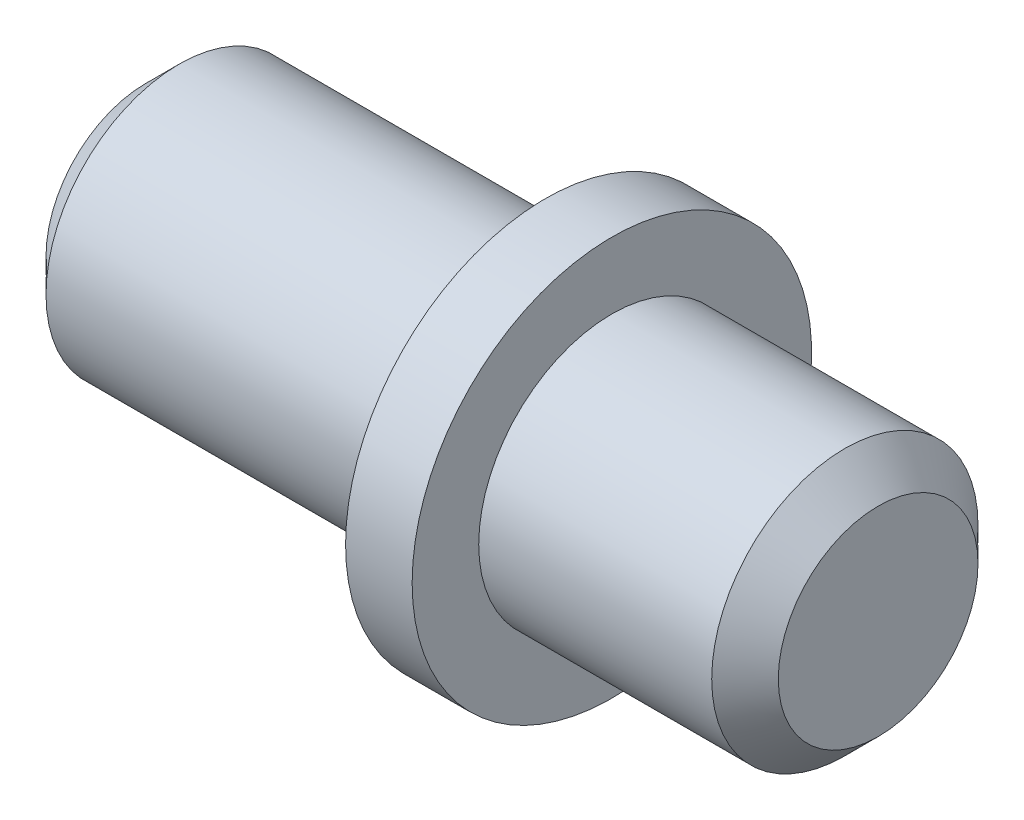
SolidWorks part; units mm, degrees
ref_plane "Plan de face" through (0, 0, 0) normal (0, 0, 1) x (1, 0, 0)
ref_plane "Plan de dessus" through (0, 0, 0) normal (0, 1, 0) x (1, 0, 0)
ref_plane "Plan de droite" through (0, 0, 0) normal (1, 0, 0) x (0, 0, -1)
sketch "Esquisse1" plane through (0, 0, 0) normal (0, 0, 1) x (1, 0, 0)
  line L0 (0, 0) -> (22.9545, 0) construction
  line L1 (0, 0) -> (0, 2)
  line L2 (0, 2) -> (-4, 2)
  line L3 (-4, 2) -> (-4, 3)
  line L4 (-4, 3) -> (-5, 3)
  line L5 (-5, 3) -> (-5, 2)
  line L6 (-5, 2) -> (-11, 2)
  line L7 (-11, 2) -> (-11, 0)
  line L8 (-11, 0) -> (0, 0)
  dimension "D1" = 4
  dimension "D2" = 4
  dimension "D3" = 6
  dimension "D4" = 4
  dimension "D5" = 11
  dimension "D6" = 6
revolve "Révolution1" add sketch "Esquisse1" angle 360 about L0
chamfer "Chanfrein1" distance 0.5 angle 45 2 edges at (-11, 0, 2) (0, 0, 2)
